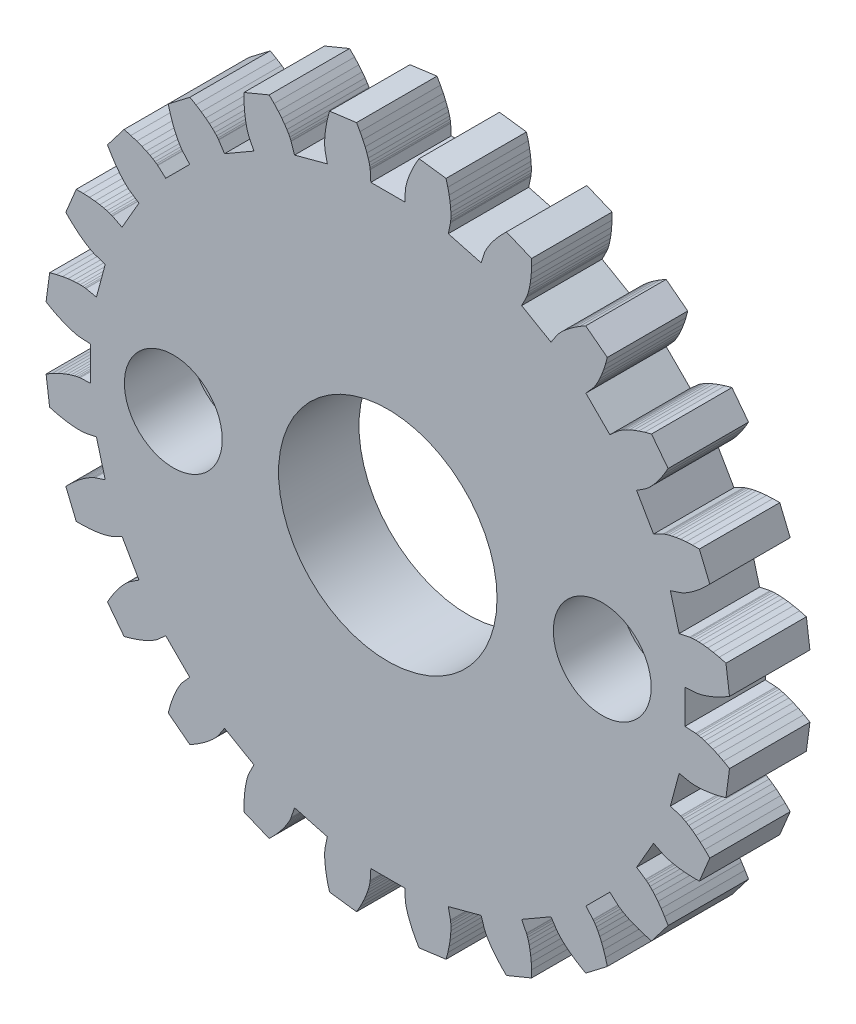
SolidWorks part; units mm, degrees
material "ABS"
ref_plane "Front Plane" through (0, 0, 0) normal (0, 0, 1) x (1, 0, 0)
ref_plane "Top Plane" through (0, 0, 0) normal (0, 1, 0) x (1, 0, 0)
ref_plane "Right Plane" through (0, 0, 0) normal (1, 0, 0) x (0, 0, -1)
sketch "Model" plane through (0, 0, 0) normal (0, 0, 1) x (1, 0, 0)
  line L0 (11.4813, -0.6559) -> (11.0819, -0.6331)
  line L1 (11.0819, -0.6331) -> (11.0819, 0.6331)
  line L2 (11.4813, 0.6559) -> (11.0819, 0.6331)
  line L3 (11.4813, 0.6559) -> (11.495, 0.6571)
  line L4 (11.495, 0.6571) -> (11.5358, 0.6626)
  line L5 (11.5358, 0.6626) -> (11.6033, 0.6749)
  line L6 (11.6033, 0.6749) -> (11.697, 0.6968)
  line L7 (11.697, 0.6968) -> (11.8158, 0.7307)
  line L8 (11.8158, 0.7307) -> (11.9589, 0.7792)
  line L9 (11.9589, 0.7792) -> (12.125, 0.8446)
  line L10 (12.125, 0.8446) -> (12.3128, 0.9294)
  line L11 (12.3128, 0.9294) -> (12.5206, 1.0358)
  line L12 (12.5206, 1.0358) -> (12.7468, 1.1658)
  line L13 (11.2598, 2.338) -> (11.2734, 2.3404)
  line L14 (11.2734, 2.3404) -> (11.3142, 2.3457)
  line L15 (11.3142, 2.3457) -> (11.3827, 2.3512)
  line L16 (11.3827, 2.3512) -> (11.4787, 2.3543)
  line L17 (11.4787, 2.3543) -> (11.6023, 2.3524)
  line L18 (11.6023, 2.3524) -> (11.7531, 2.3426)
  line L19 (11.7531, 2.3426) -> (11.9305, 2.3223)
  line L20 (11.9305, 2.3223) -> (12.1338, 2.289)
  line L21 (12.1338, 2.289) -> (12.362, 2.2401)
  line L22 (12.362, 2.2401) -> (12.6142, 2.173)
  line L23 (12.7468, 1.1658) -> (12.6142, 2.173)
  line L24 (11.2598, 2.338) -> (10.8682, 2.2567)
  line L25 (10.8682, 2.2567) -> (10.5405, 3.4797)
  line L26 (10.9203, 3.6051) -> (10.5405, 3.4797)
  line L27 (10.9203, 3.6051) -> (10.9332, 3.6098)
  line L28 (10.9332, 3.6098) -> (10.9712, 3.6257)
  line L29 (10.9712, 3.6257) -> (11.0333, 3.6551)
  line L30 (11.0333, 3.6551) -> (11.1181, 3.7004)
  line L31 (11.1181, 3.7004) -> (11.2241, 3.764)
  line L32 (11.2241, 3.764) -> (11.3497, 3.8478)
  line L33 (11.3497, 3.8478) -> (11.4933, 3.954)
  line L34 (11.4933, 3.954) -> (11.6527, 4.0845)
  line L35 (11.6527, 4.0845) -> (11.8259, 4.241)
  line L36 (11.8259, 4.241) -> (12.0107, 4.4252)
  line L37 (10.271, 5.1726) -> (10.2835, 5.1784)
  line L38 (10.2835, 5.1784) -> (10.3216, 5.1941)
  line L39 (10.3216, 5.1941) -> (10.3863, 5.2172)
  line L40 (10.3863, 5.2172) -> (10.4783, 5.245)
  line L41 (10.4783, 5.245) -> (10.5981, 5.2751)
  line L42 (10.5981, 5.2751) -> (10.7463, 5.3047)
  line L43 (10.7463, 5.3047) -> (10.9229, 5.331)
  line L44 (10.9229, 5.331) -> (11.1279, 5.3515)
  line L45 (11.1279, 5.3515) -> (11.361, 5.3633)
  line L46 (11.361, 5.3633) -> (11.622, 5.3638)
  line L47 (12.0107, 4.4252) -> (11.622, 5.3638)
  line L48 (10.271, 5.1726) -> (9.9138, 4.9927)
  line L49 (9.9138, 4.9927) -> (9.2807, 6.0892)
  line L50 (9.6151, 6.3087) -> (9.2807, 6.0892)
  line L51 (9.6151, 6.3087) -> (9.6264, 6.3166)
  line L52 (9.6264, 6.3166) -> (9.659, 6.3417)
  line L53 (9.659, 6.3417) -> (9.7113, 6.3862)
  line L54 (9.7113, 6.3862) -> (9.7815, 6.4519)
  line L55 (9.7815, 6.4519) -> (9.8675, 6.5407)
  line L56 (9.8675, 6.5407) -> (9.9671, 6.6542)
  line L57 (9.9671, 6.6542) -> (10.0783, 6.794)
  line L58 (10.0783, 6.794) -> (10.1985, 6.9613)
  line L59 (10.1985, 6.9613) -> (10.3253, 7.1573)
  line L60 (10.3253, 7.1573) -> (10.4561, 7.383)
  line L61 (8.5823, 7.6547) -> (8.5928, 7.6635)
  line L62 (8.5928, 7.6635) -> (8.6256, 7.6885)
  line L63 (8.6256, 7.6885) -> (8.6821, 7.7275)
  line L64 (8.6821, 7.7275) -> (8.7637, 7.7783)
  line L65 (8.7637, 7.7783) -> (8.8717, 7.8384)
  line L66 (8.8717, 7.8384) -> (9.0072, 7.9053)
  line L67 (9.0072, 7.9053) -> (9.1709, 7.9764)
  line L68 (9.1709, 7.9764) -> (9.3636, 8.0492)
  line L69 (9.3636, 8.0492) -> (9.5858, 8.121)
  line L70 (9.5858, 8.121) -> (9.8377, 8.189)
  line L71 (10.4561, 7.383) -> (9.8377, 8.189)
  line L72 (8.5823, 7.6547) -> (8.2838, 7.3885)
  line L73 (8.2838, 7.3885) -> (7.3885, 8.2838)
  line L74 (7.6547, 8.5823) -> (7.3885, 8.2838)
  line L75 (7.6547, 8.5823) -> (7.6635, 8.5928)
  line L76 (7.6635, 8.5928) -> (7.6885, 8.6256)
  line L77 (7.6885, 8.6256) -> (7.7275, 8.6821)
  line L78 (7.7275, 8.6821) -> (7.7783, 8.7637)
  line L79 (7.7783, 8.7637) -> (7.8384, 8.8717)
  line L80 (7.8384, 8.8717) -> (7.9053, 9.0072)
  line L81 (7.9053, 9.0072) -> (7.9764, 9.1709)
  line L82 (7.9764, 9.1709) -> (8.0492, 9.3636)
  line L83 (8.0492, 9.3636) -> (8.121, 9.5858)
  line L84 (8.121, 9.5858) -> (8.189, 9.8377)
  line L85 (6.3087, 9.6151) -> (6.3166, 9.6264)
  line L86 (6.3166, 9.6264) -> (6.3417, 9.659)
  line L87 (6.3417, 9.659) -> (6.3862, 9.7113)
  line L88 (6.3862, 9.7113) -> (6.4519, 9.7815)
  line L89 (6.4519, 9.7815) -> (6.5407, 9.8675)
  line L90 (6.5407, 9.8675) -> (6.6542, 9.9671)
  line L91 (6.6542, 9.9671) -> (6.794, 10.0783)
  line L92 (6.794, 10.0783) -> (6.9613, 10.1985)
  line L93 (6.9613, 10.1985) -> (7.1573, 10.3253)
  line L94 (7.1573, 10.3253) -> (7.383, 10.4561)
  line L95 (8.189, 9.8377) -> (7.383, 10.4561)
  line L96 (6.3087, 9.6151) -> (6.0892, 9.2807)
  line L97 (6.0892, 9.2807) -> (4.9927, 9.9138)
  line L98 (5.1726, 10.271) -> (4.9927, 9.9138)
  line L99 (5.1726, 10.271) -> (5.1784, 10.2835)
  line L100 (5.1784, 10.2835) -> (5.1941, 10.3216)
  line L101 (5.1941, 10.3216) -> (5.2172, 10.3863)
  line L102 (5.2172, 10.3863) -> (5.245, 10.4783)
  line L103 (5.245, 10.4783) -> (5.2751, 10.5981)
  line L104 (5.2751, 10.5981) -> (5.3047, 10.7463)
  line L105 (5.3047, 10.7463) -> (5.331, 10.9229)
  line L106 (5.331, 10.9229) -> (5.3515, 11.1279)
  line L107 (5.3515, 11.1279) -> (5.3633, 11.361)
  line L108 (5.3633, 11.361) -> (5.3638, 11.622)
  line L109 (3.6051, 10.9203) -> (3.6098, 10.9332)
  line L110 (3.6098, 10.9332) -> (3.6257, 10.9712)
  line L111 (3.6257, 10.9712) -> (3.6551, 11.0333)
  line L112 (3.6551, 11.0333) -> (3.7004, 11.1181)
  line L113 (3.7004, 11.1181) -> (3.764, 11.2241)
  line L114 (3.764, 11.2241) -> (3.8478, 11.3497)
  line L115 (3.8478, 11.3497) -> (3.954, 11.4933)
  line L116 (3.954, 11.4933) -> (4.0845, 11.6527)
  line L117 (4.0845, 11.6527) -> (4.241, 11.8259)
  line L118 (4.241, 11.8259) -> (4.4252, 12.0107)
  line L119 (5.3638, 11.622) -> (4.4252, 12.0107)
  line L120 (3.6051, 10.9203) -> (3.4797, 10.5405)
  line L121 (3.4797, 10.5405) -> (2.2567, 10.8682)
  line L122 (2.338, 11.2598) -> (2.2567, 10.8682)
  line L123 (2.338, 11.2598) -> (2.3404, 11.2734)
  line L124 (2.3404, 11.2734) -> (2.3457, 11.3142)
  line L125 (2.3457, 11.3142) -> (2.3512, 11.3827)
  line L126 (2.3512, 11.3827) -> (2.3543, 11.4787)
  line L127 (2.3543, 11.4787) -> (2.3524, 11.6023)
  line L128 (2.3524, 11.6023) -> (2.3426, 11.7531)
  line L129 (2.3426, 11.7531) -> (2.3223, 11.9305)
  line L130 (2.3223, 11.9305) -> (2.289, 12.1338)
  line L131 (2.289, 12.1338) -> (2.2401, 12.362)
  line L132 (2.2401, 12.362) -> (2.173, 12.6142)
  line L133 (0.6559, 11.4813) -> (0.6571, 11.495)
  line L134 (0.6571, 11.495) -> (0.6626, 11.5358)
  line L135 (0.6626, 11.5358) -> (0.6749, 11.6033)
  line L136 (0.6749, 11.6033) -> (0.6968, 11.697)
  line L137 (0.6968, 11.697) -> (0.7307, 11.8158)
  line L138 (0.7307, 11.8158) -> (0.7792, 11.9589)
  line L139 (0.7792, 11.9589) -> (0.8446, 12.125)
  line L140 (0.8446, 12.125) -> (0.9294, 12.3128)
  line L141 (0.9294, 12.3128) -> (1.0358, 12.5206)
  line L142 (1.0358, 12.5206) -> (1.1658, 12.7468)
  line L143 (2.173, 12.6142) -> (1.1658, 12.7468)
  line L144 (0.6559, 11.4813) -> (0.6331, 11.0819)
  line L145 (0.6331, 11.0819) -> (-0.6331, 11.0819)
  line L146 (-0.6559, 11.4813) -> (-0.6331, 11.0819)
  line L147 (-0.6559, 11.4813) -> (-0.6571, 11.495)
  line L148 (-0.6571, 11.495) -> (-0.6626, 11.5358)
  line L149 (-0.6626, 11.5358) -> (-0.6749, 11.6033)
  line L150 (-0.6749, 11.6033) -> (-0.6968, 11.697)
  line L151 (-0.6968, 11.697) -> (-0.7307, 11.8158)
  line L152 (-0.7307, 11.8158) -> (-0.7792, 11.9589)
  line L153 (-0.7792, 11.9589) -> (-0.8446, 12.125)
  line L154 (-0.8446, 12.125) -> (-0.9294, 12.3128)
  line L155 (-0.9294, 12.3128) -> (-1.0358, 12.5206)
  line L156 (-1.0358, 12.5206) -> (-1.1658, 12.7468)
  line L157 (-2.338, 11.2598) -> (-2.3404, 11.2734)
  line L158 (-2.3404, 11.2734) -> (-2.3457, 11.3142)
  line L159 (-2.3457, 11.3142) -> (-2.3512, 11.3827)
  line L160 (-2.3512, 11.3827) -> (-2.3543, 11.4787)
  line L161 (-2.3543, 11.4787) -> (-2.3524, 11.6023)
  line L162 (-2.3524, 11.6023) -> (-2.3426, 11.7531)
  line L163 (-2.3426, 11.7531) -> (-2.3223, 11.9305)
  line L164 (-2.3223, 11.9305) -> (-2.289, 12.1338)
  line L165 (-2.289, 12.1338) -> (-2.2401, 12.362)
  line L166 (-2.2401, 12.362) -> (-2.173, 12.6142)
  line L167 (-1.1658, 12.7468) -> (-2.173, 12.6142)
  line L168 (-2.338, 11.2598) -> (-2.2567, 10.8682)
  line L169 (-2.2567, 10.8682) -> (-3.4797, 10.5405)
  line L170 (-3.6051, 10.9203) -> (-3.4797, 10.5405)
  line L171 (-3.6051, 10.9203) -> (-3.6098, 10.9332)
  line L172 (-3.6098, 10.9332) -> (-3.6257, 10.9712)
  line L173 (-3.6257, 10.9712) -> (-3.6551, 11.0333)
  line L174 (-3.6551, 11.0333) -> (-3.7004, 11.1181)
  line L175 (-3.7004, 11.1181) -> (-3.764, 11.2241)
  line L176 (-3.764, 11.2241) -> (-3.8478, 11.3497)
  line L177 (-3.8478, 11.3497) -> (-3.954, 11.4933)
  line L178 (-3.954, 11.4933) -> (-4.0845, 11.6527)
  line L179 (-4.0845, 11.6527) -> (-4.241, 11.8259)
  line L180 (-4.241, 11.8259) -> (-4.4252, 12.0107)
  line L181 (-5.1726, 10.271) -> (-5.1784, 10.2835)
  line L182 (-5.1784, 10.2835) -> (-5.1941, 10.3216)
  line L183 (-5.1941, 10.3216) -> (-5.2172, 10.3863)
  line L184 (-5.2172, 10.3863) -> (-5.245, 10.4783)
  line L185 (-5.245, 10.4783) -> (-5.2751, 10.5981)
  line L186 (-5.2751, 10.5981) -> (-5.3047, 10.7463)
  line L187 (-5.3047, 10.7463) -> (-5.331, 10.9229)
  line L188 (-5.331, 10.9229) -> (-5.3515, 11.1279)
  line L189 (-5.3515, 11.1279) -> (-5.3633, 11.361)
  line L190 (-5.3633, 11.361) -> (-5.3638, 11.622)
  line L191 (-4.4252, 12.0107) -> (-5.3638, 11.622)
  line L192 (-5.1726, 10.271) -> (-4.9927, 9.9138)
  line L193 (-4.9927, 9.9138) -> (-6.0892, 9.2807)
  line L194 (-6.3087, 9.6151) -> (-6.0892, 9.2807)
  line L195 (-6.3087, 9.6151) -> (-6.3166, 9.6264)
  line L196 (-6.3166, 9.6264) -> (-6.3417, 9.659)
  line L197 (-6.3417, 9.659) -> (-6.3862, 9.7113)
  line L198 (-6.3862, 9.7113) -> (-6.4519, 9.7815)
  line L199 (-6.4519, 9.7815) -> (-6.5407, 9.8675)
  line L200 (-6.5407, 9.8675) -> (-6.6542, 9.9671)
  line L201 (-6.6542, 9.9671) -> (-6.794, 10.0783)
  line L202 (-6.794, 10.0783) -> (-6.9613, 10.1985)
  line L203 (-6.9613, 10.1985) -> (-7.1573, 10.3253)
  line L204 (-7.1573, 10.3253) -> (-7.383, 10.4561)
  line L205 (-7.6547, 8.5823) -> (-7.6635, 8.5928)
  line L206 (-7.6635, 8.5928) -> (-7.6885, 8.6256)
  line L207 (-7.6885, 8.6256) -> (-7.7275, 8.6821)
  line L208 (-7.7275, 8.6821) -> (-7.7783, 8.7637)
  line L209 (-7.7783, 8.7637) -> (-7.8384, 8.8717)
  line L210 (-7.8384, 8.8717) -> (-7.9053, 9.0072)
  line L211 (-7.9053, 9.0072) -> (-7.9764, 9.1709)
  line L212 (-7.9764, 9.1709) -> (-8.0492, 9.3636)
  line L213 (-8.0492, 9.3636) -> (-8.121, 9.5858)
  line L214 (-8.121, 9.5858) -> (-8.189, 9.8377)
  line L215 (-7.383, 10.4561) -> (-8.189, 9.8377)
  line L216 (-7.6547, 8.5823) -> (-7.3885, 8.2838)
  line L217 (-7.3885, 8.2838) -> (-8.2838, 7.3885)
  line L218 (-8.5823, 7.6547) -> (-8.2838, 7.3885)
  line L219 (-8.5823, 7.6547) -> (-8.5928, 7.6635)
  line L220 (-8.5928, 7.6635) -> (-8.6256, 7.6885)
  line L221 (-8.6256, 7.6885) -> (-8.6821, 7.7275)
  line L222 (-8.6821, 7.7275) -> (-8.7637, 7.7783)
  line L223 (-8.7637, 7.7783) -> (-8.8717, 7.8384)
  line L224 (-8.8717, 7.8384) -> (-9.0072, 7.9053)
  line L225 (-9.0072, 7.9053) -> (-9.1709, 7.9764)
  line L226 (-9.1709, 7.9764) -> (-9.3636, 8.0492)
  line L227 (-9.3636, 8.0492) -> (-9.5858, 8.121)
  line L228 (-9.5858, 8.121) -> (-9.8377, 8.189)
  line L229 (-9.6151, 6.3087) -> (-9.6264, 6.3166)
  line L230 (-9.6264, 6.3166) -> (-9.659, 6.3417)
  line L231 (-9.659, 6.3417) -> (-9.7113, 6.3862)
  line L232 (-9.7113, 6.3862) -> (-9.7815, 6.4519)
  line L233 (-9.7815, 6.4519) -> (-9.8675, 6.5407)
  line L234 (-9.8675, 6.5407) -> (-9.9671, 6.6542)
  line L235 (-9.9671, 6.6542) -> (-10.0783, 6.794)
  line L236 (-10.0783, 6.794) -> (-10.1985, 6.9613)
  line L237 (-10.1985, 6.9613) -> (-10.3253, 7.1573)
  line L238 (-10.3253, 7.1573) -> (-10.4561, 7.383)
  line L239 (-9.8377, 8.189) -> (-10.4561, 7.383)
  line L240 (-9.6151, 6.3087) -> (-9.2807, 6.0892)
  line L241 (-9.2807, 6.0892) -> (-9.9138, 4.9927)
  line L242 (-10.271, 5.1726) -> (-9.9138, 4.9927)
  line L243 (-10.271, 5.1726) -> (-10.2835, 5.1784)
  line L244 (-10.2835, 5.1784) -> (-10.3216, 5.1941)
  line L245 (-10.3216, 5.1941) -> (-10.3863, 5.2172)
  line L246 (-10.3863, 5.2172) -> (-10.4783, 5.245)
  line L247 (-10.4783, 5.245) -> (-10.5981, 5.2751)
  line L248 (-10.5981, 5.2751) -> (-10.7463, 5.3047)
  line L249 (-10.7463, 5.3047) -> (-10.9229, 5.331)
  line L250 (-10.9229, 5.331) -> (-11.1279, 5.3515)
  line L251 (-11.1279, 5.3515) -> (-11.361, 5.3633)
  line L252 (-11.361, 5.3633) -> (-11.622, 5.3638)
  line L253 (-10.9203, 3.6051) -> (-10.9332, 3.6098)
  line L254 (-10.9332, 3.6098) -> (-10.9712, 3.6257)
  line L255 (-10.9712, 3.6257) -> (-11.0333, 3.6551)
  line L256 (-11.0333, 3.6551) -> (-11.1181, 3.7004)
  line L257 (-11.1181, 3.7004) -> (-11.2241, 3.764)
  line L258 (-11.2241, 3.764) -> (-11.3497, 3.8478)
  line L259 (-11.3497, 3.8478) -> (-11.4933, 3.954)
  line L260 (-11.4933, 3.954) -> (-11.6527, 4.0845)
  line L261 (-11.6527, 4.0845) -> (-11.8259, 4.241)
  line L262 (-11.8259, 4.241) -> (-12.0107, 4.4252)
  line L263 (-11.622, 5.3638) -> (-12.0107, 4.4252)
  line L264 (-10.9203, 3.6051) -> (-10.5405, 3.4797)
  line L265 (-10.5405, 3.4797) -> (-10.8682, 2.2567)
  line L266 (-11.2598, 2.338) -> (-10.8682, 2.2567)
  line L267 (-11.2598, 2.338) -> (-11.2734, 2.3404)
  line L268 (-11.2734, 2.3404) -> (-11.3142, 2.3457)
  line L269 (-11.3142, 2.3457) -> (-11.3827, 2.3512)
  line L270 (-11.3827, 2.3512) -> (-11.4787, 2.3543)
  line L271 (-11.4787, 2.3543) -> (-11.6023, 2.3524)
  line L272 (-11.6023, 2.3524) -> (-11.7531, 2.3426)
  line L273 (-11.7531, 2.3426) -> (-11.9305, 2.3223)
  line L274 (-11.9305, 2.3223) -> (-12.1338, 2.289)
  line L275 (-12.1338, 2.289) -> (-12.362, 2.2401)
  line L276 (-12.362, 2.2401) -> (-12.6142, 2.173)
  line L277 (-11.4813, 0.6559) -> (-11.495, 0.6571)
  line L278 (-11.495, 0.6571) -> (-11.5358, 0.6626)
  line L279 (-11.5358, 0.6626) -> (-11.6033, 0.6749)
  line L280 (-11.6033, 0.6749) -> (-11.697, 0.6968)
  line L281 (-11.697, 0.6968) -> (-11.8158, 0.7307)
  line L282 (-11.8158, 0.7307) -> (-11.9589, 0.7792)
  line L283 (-11.9589, 0.7792) -> (-12.125, 0.8446)
  line L284 (-12.125, 0.8446) -> (-12.3128, 0.9294)
  line L285 (-12.3128, 0.9294) -> (-12.5206, 1.0358)
  line L286 (-12.5206, 1.0358) -> (-12.7468, 1.1658)
  line L287 (-12.6142, 2.173) -> (-12.7468, 1.1658)
  line L288 (-11.4813, 0.6559) -> (-11.0819, 0.6331)
  line L289 (-11.0819, 0.6331) -> (-11.0819, -0.6331)
  line L290 (-11.4813, -0.6559) -> (-11.0819, -0.6331)
  line L291 (-11.4813, -0.6559) -> (-11.495, -0.6571)
  line L292 (-11.495, -0.6571) -> (-11.5358, -0.6626)
  line L293 (-11.5358, -0.6626) -> (-11.6033, -0.6749)
  line L294 (-11.6033, -0.6749) -> (-11.697, -0.6968)
  line L295 (-11.697, -0.6968) -> (-11.8158, -0.7307)
  line L296 (-11.8158, -0.7307) -> (-11.9589, -0.7792)
  line L297 (-11.9589, -0.7792) -> (-12.125, -0.8446)
  line L298 (-12.125, -0.8446) -> (-12.3128, -0.9294)
  line L299 (-12.3128, -0.9294) -> (-12.5206, -1.0358)
  line L300 (-12.5206, -1.0358) -> (-12.7468, -1.1658)
  line L301 (-11.2598, -2.338) -> (-11.2734, -2.3404)
  line L302 (-11.2734, -2.3404) -> (-11.3142, -2.3457)
  line L303 (-11.3142, -2.3457) -> (-11.3827, -2.3512)
  line L304 (-11.3827, -2.3512) -> (-11.4787, -2.3543)
  line L305 (-11.4787, -2.3543) -> (-11.6023, -2.3524)
  line L306 (-11.6023, -2.3524) -> (-11.7531, -2.3426)
  line L307 (-11.7531, -2.3426) -> (-11.9305, -2.3223)
  line L308 (-11.9305, -2.3223) -> (-12.1338, -2.289)
  line L309 (-12.1338, -2.289) -> (-12.362, -2.2401)
  line L310 (-12.362, -2.2401) -> (-12.6142, -2.173)
  line L311 (-12.7468, -1.1658) -> (-12.6142, -2.173)
  line L312 (-11.2598, -2.338) -> (-10.8682, -2.2567)
  line L313 (-10.8682, -2.2567) -> (-10.5405, -3.4797)
  line L314 (-10.9203, -3.6051) -> (-10.5405, -3.4797)
  line L315 (-10.9203, -3.6051) -> (-10.9332, -3.6098)
  line L316 (-10.9332, -3.6098) -> (-10.9712, -3.6257)
  line L317 (-10.9712, -3.6257) -> (-11.0333, -3.6551)
  line L318 (-11.0333, -3.6551) -> (-11.1181, -3.7004)
  line L319 (-11.1181, -3.7004) -> (-11.2241, -3.764)
  line L320 (-11.2241, -3.764) -> (-11.3497, -3.8478)
  line L321 (-11.3497, -3.8478) -> (-11.4933, -3.954)
  line L322 (-11.4933, -3.954) -> (-11.6527, -4.0845)
  line L323 (-11.6527, -4.0845) -> (-11.8259, -4.241)
  line L324 (-11.8259, -4.241) -> (-12.0107, -4.4252)
  line L325 (-10.271, -5.1726) -> (-10.2835, -5.1784)
  line L326 (-10.2835, -5.1784) -> (-10.3216, -5.1941)
  line L327 (-10.3216, -5.1941) -> (-10.3863, -5.2172)
  line L328 (-10.3863, -5.2172) -> (-10.4783, -5.245)
  line L329 (-10.4783, -5.245) -> (-10.5981, -5.2751)
  line L330 (-10.5981, -5.2751) -> (-10.7463, -5.3047)
  line L331 (-10.7463, -5.3047) -> (-10.9229, -5.331)
  line L332 (-10.9229, -5.331) -> (-11.1279, -5.3515)
  line L333 (-11.1279, -5.3515) -> (-11.361, -5.3633)
  line L334 (-11.361, -5.3633) -> (-11.622, -5.3638)
  line L335 (-12.0107, -4.4252) -> (-11.622, -5.3638)
  line L336 (-10.271, -5.1726) -> (-9.9138, -4.9927)
  line L337 (-9.9138, -4.9927) -> (-9.2807, -6.0892)
  line L338 (-9.6151, -6.3087) -> (-9.2807, -6.0892)
  line L339 (-9.6151, -6.3087) -> (-9.6264, -6.3166)
  line L340 (-9.6264, -6.3166) -> (-9.659, -6.3417)
  line L341 (-9.659, -6.3417) -> (-9.7113, -6.3862)
  line L342 (-9.7113, -6.3862) -> (-9.7815, -6.4519)
  line L343 (-9.7815, -6.4519) -> (-9.8675, -6.5407)
  line L344 (-9.8675, -6.5407) -> (-9.9671, -6.6542)
  line L345 (-9.9671, -6.6542) -> (-10.0783, -6.794)
  line L346 (-10.0783, -6.794) -> (-10.1985, -6.9613)
  line L347 (-10.1985, -6.9613) -> (-10.3253, -7.1573)
  line L348 (-10.3253, -7.1573) -> (-10.4561, -7.383)
  line L349 (-8.5823, -7.6547) -> (-8.5928, -7.6635)
  line L350 (-8.5928, -7.6635) -> (-8.6256, -7.6885)
  line L351 (-8.6256, -7.6885) -> (-8.6821, -7.7275)
  line L352 (-8.6821, -7.7275) -> (-8.7637, -7.7783)
  line L353 (-8.7637, -7.7783) -> (-8.8717, -7.8384)
  line L354 (-8.8717, -7.8384) -> (-9.0072, -7.9053)
  line L355 (-9.0072, -7.9053) -> (-9.1709, -7.9764)
  line L356 (-9.1709, -7.9764) -> (-9.3636, -8.0492)
  line L357 (-9.3636, -8.0492) -> (-9.5858, -8.121)
  line L358 (-9.5858, -8.121) -> (-9.8377, -8.189)
  line L359 (-10.4561, -7.383) -> (-9.8377, -8.189)
  line L360 (-8.5823, -7.6547) -> (-8.2838, -7.3885)
  line L361 (-8.2838, -7.3885) -> (-7.3885, -8.2838)
  line L362 (-7.6547, -8.5823) -> (-7.3885, -8.2838)
  line L363 (-7.6547, -8.5823) -> (-7.6635, -8.5928)
  line L364 (-7.6635, -8.5928) -> (-7.6885, -8.6256)
  line L365 (-7.6885, -8.6256) -> (-7.7275, -8.6821)
  line L366 (-7.7275, -8.6821) -> (-7.7783, -8.7637)
  line L367 (-7.7783, -8.7637) -> (-7.8384, -8.8717)
  line L368 (-7.8384, -8.8717) -> (-7.9053, -9.0072)
  line L369 (-7.9053, -9.0072) -> (-7.9764, -9.1709)
  line L370 (-7.9764, -9.1709) -> (-8.0492, -9.3636)
  line L371 (-8.0492, -9.3636) -> (-8.121, -9.5858)
  line L372 (-8.121, -9.5858) -> (-8.189, -9.8377)
  line L373 (-6.3087, -9.6151) -> (-6.3166, -9.6264)
  line L374 (-6.3166, -9.6264) -> (-6.3417, -9.659)
  line L375 (-6.3417, -9.659) -> (-6.3862, -9.7113)
  line L376 (-6.3862, -9.7113) -> (-6.4519, -9.7815)
  line L377 (-6.4519, -9.7815) -> (-6.5407, -9.8675)
  line L378 (-6.5407, -9.8675) -> (-6.6542, -9.9671)
  line L379 (-6.6542, -9.9671) -> (-6.794, -10.0783)
  line L380 (-6.794, -10.0783) -> (-6.9613, -10.1985)
  line L381 (-6.9613, -10.1985) -> (-7.1573, -10.3253)
  line L382 (-7.1573, -10.3253) -> (-7.383, -10.4561)
  line L383 (-8.189, -9.8377) -> (-7.383, -10.4561)
  line L384 (-6.3087, -9.6151) -> (-6.0892, -9.2807)
  line L385 (-6.0892, -9.2807) -> (-4.9927, -9.9138)
  line L386 (-5.1726, -10.271) -> (-4.9927, -9.9138)
  line L387 (-5.1726, -10.271) -> (-5.1784, -10.2835)
  line L388 (-5.1784, -10.2835) -> (-5.1941, -10.3216)
  line L389 (-5.1941, -10.3216) -> (-5.2172, -10.3863)
  line L390 (-5.2172, -10.3863) -> (-5.245, -10.4783)
  line L391 (-5.245, -10.4783) -> (-5.2751, -10.5981)
  line L392 (-5.2751, -10.5981) -> (-5.3047, -10.7463)
  line L393 (-5.3047, -10.7463) -> (-5.331, -10.9229)
  line L394 (-5.331, -10.9229) -> (-5.3515, -11.1279)
  line L395 (-5.3515, -11.1279) -> (-5.3633, -11.361)
  line L396 (-5.3633, -11.361) -> (-5.3638, -11.622)
  line L397 (-3.6051, -10.9203) -> (-3.6098, -10.9332)
  line L398 (-3.6098, -10.9332) -> (-3.6257, -10.9712)
  line L399 (-3.6257, -10.9712) -> (-3.6551, -11.0333)
  line L400 (-3.6551, -11.0333) -> (-3.7004, -11.1181)
  line L401 (-3.7004, -11.1181) -> (-3.764, -11.2241)
  line L402 (-3.764, -11.2241) -> (-3.8478, -11.3497)
  line L403 (-3.8478, -11.3497) -> (-3.954, -11.4933)
  line L404 (-3.954, -11.4933) -> (-4.0845, -11.6527)
  line L405 (-4.0845, -11.6527) -> (-4.241, -11.8259)
  line L406 (-4.241, -11.8259) -> (-4.4252, -12.0107)
  line L407 (-5.3638, -11.622) -> (-4.4252, -12.0107)
  line L408 (-3.6051, -10.9203) -> (-3.4797, -10.5405)
  line L409 (-3.4797, -10.5405) -> (-2.2567, -10.8682)
  line L410 (-2.338, -11.2598) -> (-2.2567, -10.8682)
  line L411 (-2.338, -11.2598) -> (-2.3404, -11.2734)
  line L412 (-2.3404, -11.2734) -> (-2.3457, -11.3142)
  line L413 (-2.3457, -11.3142) -> (-2.3512, -11.3827)
  line L414 (-2.3512, -11.3827) -> (-2.3543, -11.4787)
  line L415 (-2.3543, -11.4787) -> (-2.3524, -11.6023)
  line L416 (-2.3524, -11.6023) -> (-2.3426, -11.7531)
  line L417 (-2.3426, -11.7531) -> (-2.3223, -11.9305)
  line L418 (-2.3223, -11.9305) -> (-2.289, -12.1338)
  line L419 (-2.289, -12.1338) -> (-2.2401, -12.362)
  line L420 (-2.2401, -12.362) -> (-2.173, -12.6142)
  line L421 (-0.6559, -11.4813) -> (-0.6571, -11.495)
  line L422 (-0.6571, -11.495) -> (-0.6626, -11.5358)
  line L423 (-0.6626, -11.5358) -> (-0.6749, -11.6033)
  line L424 (-0.6749, -11.6033) -> (-0.6968, -11.697)
  line L425 (-0.6968, -11.697) -> (-0.7307, -11.8158)
  line L426 (-0.7307, -11.8158) -> (-0.7792, -11.9589)
  line L427 (-0.7792, -11.9589) -> (-0.8446, -12.125)
  line L428 (-0.8446, -12.125) -> (-0.9294, -12.3128)
  line L429 (-0.9294, -12.3128) -> (-1.0358, -12.5206)
  line L430 (-1.0358, -12.5206) -> (-1.1658, -12.7468)
  line L431 (-2.173, -12.6142) -> (-1.1658, -12.7468)
  line L432 (-0.6559, -11.4813) -> (-0.6331, -11.0819)
  line L433 (-0.6331, -11.0819) -> (0.6331, -11.0819)
  line L434 (0.6559, -11.4813) -> (0.6331, -11.0819)
  line L435 (0.6559, -11.4813) -> (0.6571, -11.495)
  line L436 (0.6571, -11.495) -> (0.6626, -11.5358)
  line L437 (0.6626, -11.5358) -> (0.6749, -11.6033)
  line L438 (0.6749, -11.6033) -> (0.6968, -11.697)
  line L439 (0.6968, -11.697) -> (0.7307, -11.8158)
  line L440 (0.7307, -11.8158) -> (0.7792, -11.9589)
  line L441 (0.7792, -11.9589) -> (0.8446, -12.125)
  line L442 (0.8446, -12.125) -> (0.9294, -12.3128)
  line L443 (0.9294, -12.3128) -> (1.0358, -12.5206)
  line L444 (1.0358, -12.5206) -> (1.1658, -12.7468)
  line L445 (2.338, -11.2598) -> (2.3404, -11.2734)
  line L446 (2.3404, -11.2734) -> (2.3457, -11.3142)
  line L447 (2.3457, -11.3142) -> (2.3512, -11.3827)
  line L448 (2.3512, -11.3827) -> (2.3543, -11.4787)
  line L449 (2.3543, -11.4787) -> (2.3524, -11.6023)
  line L450 (2.3524, -11.6023) -> (2.3426, -11.7531)
  line L451 (2.3426, -11.7531) -> (2.3223, -11.9305)
  line L452 (2.3223, -11.9305) -> (2.289, -12.1338)
  line L453 (2.289, -12.1338) -> (2.2401, -12.362)
  line L454 (2.2401, -12.362) -> (2.173, -12.6142)
  line L455 (1.1658, -12.7468) -> (2.173, -12.6142)
  line L456 (2.338, -11.2598) -> (2.2567, -10.8682)
  line L457 (2.2567, -10.8682) -> (3.4797, -10.5405)
  line L458 (3.6051, -10.9203) -> (3.4797, -10.5405)
  line L459 (3.6051, -10.9203) -> (3.6098, -10.9332)
  line L460 (3.6098, -10.9332) -> (3.6257, -10.9712)
  line L461 (3.6257, -10.9712) -> (3.6551, -11.0333)
  line L462 (3.6551, -11.0333) -> (3.7004, -11.1181)
  line L463 (3.7004, -11.1181) -> (3.764, -11.2241)
  line L464 (3.764, -11.2241) -> (3.8478, -11.3497)
  line L465 (3.8478, -11.3497) -> (3.954, -11.4933)
  line L466 (3.954, -11.4933) -> (4.0845, -11.6527)
  line L467 (4.0845, -11.6527) -> (4.241, -11.8259)
  line L468 (4.241, -11.8259) -> (4.4252, -12.0107)
  line L469 (5.1726, -10.271) -> (5.1784, -10.2835)
  line L470 (5.1784, -10.2835) -> (5.1941, -10.3216)
  line L471 (5.1941, -10.3216) -> (5.2172, -10.3863)
  line L472 (5.2172, -10.3863) -> (5.245, -10.4783)
  line L473 (5.245, -10.4783) -> (5.2751, -10.5981)
  line L474 (5.2751, -10.5981) -> (5.3047, -10.7463)
  line L475 (5.3047, -10.7463) -> (5.331, -10.9229)
  line L476 (5.331, -10.9229) -> (5.3515, -11.1279)
  line L477 (5.3515, -11.1279) -> (5.3633, -11.361)
  line L478 (5.3633, -11.361) -> (5.3638, -11.622)
  line L479 (4.4252, -12.0107) -> (5.3638, -11.622)
  line L480 (5.1726, -10.271) -> (4.9927, -9.9138)
  line L481 (4.9927, -9.9138) -> (6.0892, -9.2807)
  line L482 (6.3087, -9.6151) -> (6.0892, -9.2807)
  line L483 (6.3087, -9.6151) -> (6.3166, -9.6264)
  line L484 (6.3166, -9.6264) -> (6.3417, -9.659)
  line L485 (6.3417, -9.659) -> (6.3862, -9.7113)
  line L486 (6.3862, -9.7113) -> (6.4519, -9.7815)
  line L487 (6.4519, -9.7815) -> (6.5407, -9.8675)
  line L488 (6.5407, -9.8675) -> (6.6542, -9.9671)
  line L489 (6.6542, -9.9671) -> (6.794, -10.0783)
  line L490 (6.794, -10.0783) -> (6.9613, -10.1985)
  line L491 (6.9613, -10.1985) -> (7.1573, -10.3253)
  line L492 (7.1573, -10.3253) -> (7.383, -10.4561)
  line L493 (7.6547, -8.5823) -> (7.6635, -8.5928)
  line L494 (7.6635, -8.5928) -> (7.6885, -8.6256)
  line L495 (7.6885, -8.6256) -> (7.7275, -8.6821)
  line L496 (7.7275, -8.6821) -> (7.7783, -8.7637)
  line L497 (7.7783, -8.7637) -> (7.8384, -8.8717)
  line L498 (7.8384, -8.8717) -> (7.9053, -9.0072)
  line L499 (7.9053, -9.0072) -> (7.9764, -9.1709)
  line L500 (7.9764, -9.1709) -> (8.0492, -9.3636)
  line L501 (8.0492, -9.3636) -> (8.121, -9.5858)
  line L502 (8.121, -9.5858) -> (8.189, -9.8377)
  line L503 (7.383, -10.4561) -> (8.189, -9.8377)
  line L504 (7.6547, -8.5823) -> (7.3885, -8.2838)
  line L505 (7.3885, -8.2838) -> (8.2838, -7.3885)
  line L506 (8.5823, -7.6547) -> (8.2838, -7.3885)
  line L507 (8.5823, -7.6547) -> (8.5928, -7.6635)
  line L508 (8.5928, -7.6635) -> (8.6256, -7.6885)
  line L509 (8.6256, -7.6885) -> (8.6821, -7.7275)
  line L510 (8.6821, -7.7275) -> (8.7637, -7.7783)
  line L511 (8.7637, -7.7783) -> (8.8717, -7.8384)
  line L512 (8.8717, -7.8384) -> (9.0072, -7.9053)
  line L513 (9.0072, -7.9053) -> (9.1709, -7.9764)
  line L514 (9.1709, -7.9764) -> (9.3636, -8.0492)
  line L515 (9.3636, -8.0492) -> (9.5858, -8.121)
  line L516 (9.5858, -8.121) -> (9.8377, -8.189)
  line L517 (9.6151, -6.3087) -> (9.6264, -6.3166)
  line L518 (9.6264, -6.3166) -> (9.659, -6.3417)
  line L519 (9.659, -6.3417) -> (9.7113, -6.3862)
  line L520 (9.7113, -6.3862) -> (9.7815, -6.4519)
  line L521 (9.7815, -6.4519) -> (9.8675, -6.5407)
  line L522 (9.8675, -6.5407) -> (9.9671, -6.6542)
  line L523 (9.9671, -6.6542) -> (10.0783, -6.794)
  line L524 (10.0783, -6.794) -> (10.1985, -6.9613)
  line L525 (10.1985, -6.9613) -> (10.3253, -7.1573)
  line L526 (10.3253, -7.1573) -> (10.4561, -7.383)
  line L527 (9.8377, -8.189) -> (10.4561, -7.383)
  line L528 (9.6151, -6.3087) -> (9.2807, -6.0892)
  line L529 (9.2807, -6.0892) -> (9.9138, -4.9927)
  line L530 (10.271, -5.1726) -> (9.9138, -4.9927)
  line L531 (10.271, -5.1726) -> (10.2835, -5.1784)
  line L532 (10.2835, -5.1784) -> (10.3216, -5.1941)
  line L533 (10.3216, -5.1941) -> (10.3863, -5.2172)
  line L534 (10.3863, -5.2172) -> (10.4783, -5.245)
  line L535 (10.4783, -5.245) -> (10.5981, -5.2751)
  line L536 (10.5981, -5.2751) -> (10.7463, -5.3047)
  line L537 (10.7463, -5.3047) -> (10.9229, -5.331)
  line L538 (10.9229, -5.331) -> (11.1279, -5.3515)
  line L539 (11.1279, -5.3515) -> (11.361, -5.3633)
  line L540 (11.361, -5.3633) -> (11.622, -5.3638)
  line L541 (10.9203, -3.6051) -> (10.9332, -3.6098)
  line L542 (10.9332, -3.6098) -> (10.9712, -3.6257)
  line L543 (10.9712, -3.6257) -> (11.0333, -3.6551)
  line L544 (11.0333, -3.6551) -> (11.1181, -3.7004)
  line L545 (11.1181, -3.7004) -> (11.2241, -3.764)
  line L546 (11.2241, -3.764) -> (11.3497, -3.8478)
  line L547 (11.3497, -3.8478) -> (11.4933, -3.954)
  line L548 (11.4933, -3.954) -> (11.6527, -4.0845)
  line L549 (11.6527, -4.0845) -> (11.8259, -4.241)
  line L550 (11.8259, -4.241) -> (12.0107, -4.4252)
  line L551 (11.622, -5.3638) -> (12.0107, -4.4252)
  line L552 (10.9203, -3.6051) -> (10.5405, -3.4797)
  line L553 (10.5405, -3.4797) -> (10.8682, -2.2567)
  line L554 (11.2598, -2.338) -> (10.8682, -2.2567)
  line L555 (11.2598, -2.338) -> (11.2734, -2.3404)
  line L556 (11.2734, -2.3404) -> (11.3142, -2.3457)
  line L557 (11.3142, -2.3457) -> (11.3827, -2.3512)
  line L558 (11.3827, -2.3512) -> (11.4787, -2.3543)
  line L559 (11.4787, -2.3543) -> (11.6023, -2.3524)
  line L560 (11.6023, -2.3524) -> (11.7531, -2.3426)
  line L561 (11.7531, -2.3426) -> (11.9305, -2.3223)
  line L562 (11.9305, -2.3223) -> (12.1338, -2.289)
  line L563 (12.1338, -2.289) -> (12.362, -2.2401)
  line L564 (12.362, -2.2401) -> (12.6142, -2.173)
  line L565 (11.4813, -0.6559) -> (11.495, -0.6571)
  line L566 (11.495, -0.6571) -> (11.5358, -0.6626)
  line L567 (11.5358, -0.6626) -> (11.6033, -0.6749)
  line L568 (11.6033, -0.6749) -> (11.697, -0.6968)
  line L569 (11.697, -0.6968) -> (11.8158, -0.7307)
  line L570 (11.8158, -0.7307) -> (11.9589, -0.7792)
  line L571 (11.9589, -0.7792) -> (12.125, -0.8446)
  line L572 (12.125, -0.8446) -> (12.3128, -0.9294)
  line L573 (12.3128, -0.9294) -> (12.5206, -1.0358)
  line L574 (12.5206, -1.0358) -> (12.7468, -1.1658)
  line L575 (12.6142, -2.173) -> (12.7468, -1.1658)
extrude "Main Gear Body" add sketch "Model" along normal blind 3
sketch "Sketch1" plane through (0, 0, 3) normal (0, 0, 1) x (1, 0, 0)
  line L0 (-8, 0) -> (8, 0) construction
  circle A0 centre (0, 0) radius 4.075
  circle A1 centre (-8, 0) radius 1.15
  circle A2 centre (8, 0) radius 1.15
  dimension "D1" = 16
  dimension "D2" = 2.3
  dimension "D3" = 8.15
extrude "Servo Clearance" cut sketch "Sketch1" against normal through all
sketch "Sketch2" plane through (0, 0, 3) normal (0, 0, 1) x (1, 0, 0)
  circle A0 centre (8, 0) radius 1.825
  circle A1 centre (-8, 0) radius 1.825
  circle A3 centre (-8, 0) radius 1.15 construction
  circle A4 centre (8, 0) radius 1.15 construction
  dimension "D1" = 3.65
extrude "Bolt Head Clearance" cut sketch "Sketch2" against normal blind 2.5
ref_point "Point1"
equation "\"D3@Sketch1\"=8+\"print fit@values@params_print.sldprt\""
equation "\"D1@Sketch2\"=3.5+\"print fit@values@params_print.sldprt\""
